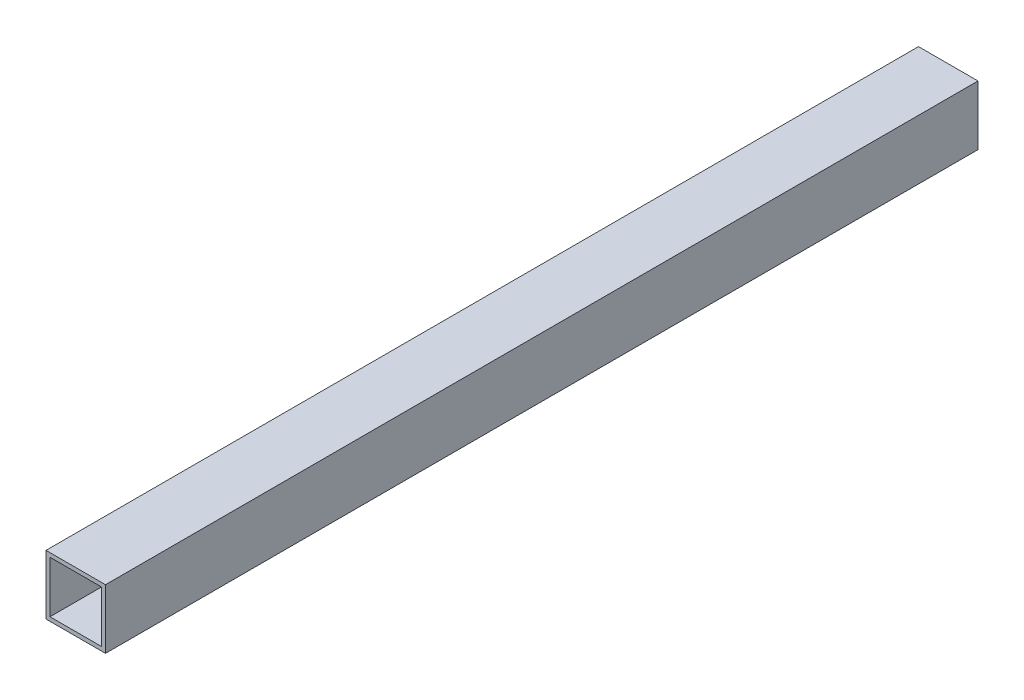
SolidWorks part; units mm, degrees
ref_plane "Front Plane" through (0, 0, 0) normal (0, 0, 1) x (1, 0, 0)
ref_plane "Top Plane" through (0, 0, 0) normal (0, 1, 0) x (1, 0, 0)
ref_plane "Right Plane" through (0, 0, 0) normal (1, 0, 0) x (0, 0, -1)
sketch "Esboço1" plane through (0, 0, 0) normal (0, 0, 1) x (1, 0, 0)
  line L1 (-4.3448, 102.2122) -> (25.6552, 102.2122)
  line L2 (-4.3448, 102.2122) -> (-4.3448, 72.2122)
  line L3 (-4.3448, 72.2122) -> (25.6552, 72.2122)
  line L4 (25.6552, 102.2122) -> (25.6552, 72.2122)
  dimension "D1" = 30
  dimension "D2" = 30
extrude "Ressalto-extrusão1" add sketch "Esboço1" along normal blind 440
shell "Casca1" thickness 2
